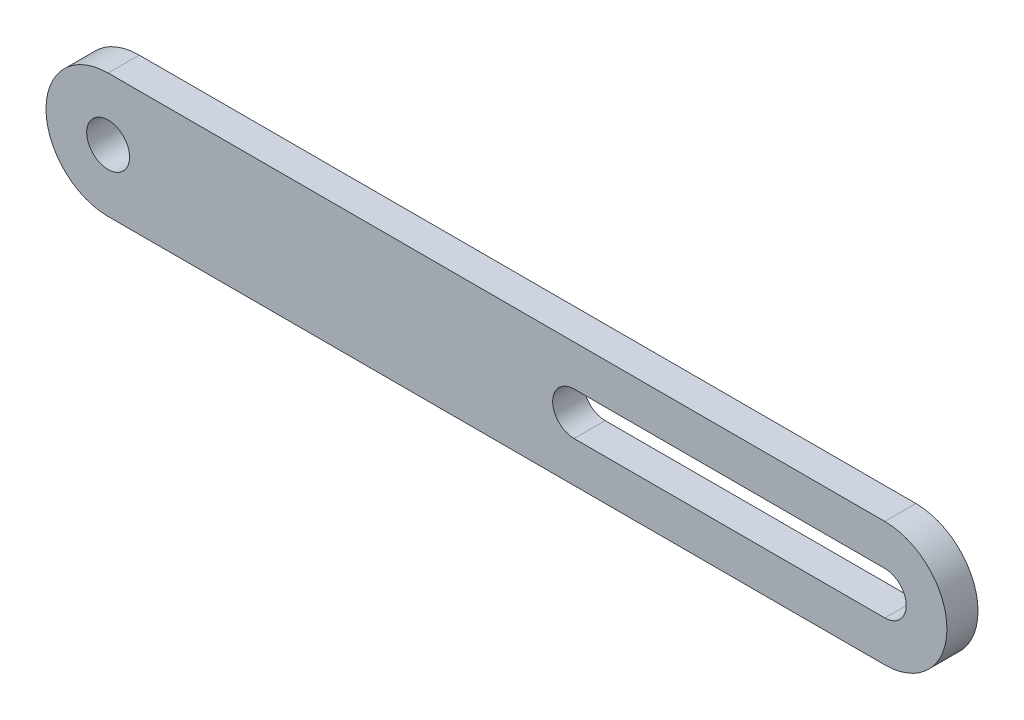
SolidWorks part; units mm, degrees
ref_plane "Front Plane" through (0, 0, 0) normal (0, 0, 1) x (1, 0, 0)
ref_plane "Top Plane" through (0, 0, 0) normal (0, 1, 0) x (1, 0, 0)
ref_plane "Right Plane" through (0, 0, 0) normal (1, 0, 0) x (0, 0, -1)
sketch "Sketch1" plane through (0, 0, 0) normal (0, 0, 1) x (1, 0, 0)
  line L0 (0, 0) -> (63.5, 0) construction
  line L1 (0, 5.08) -> (63.5, 5.08)
  line L2 (0, -5.08) -> (63.5, -5.08)
  arc A0 (0, 5.08) -> (0, -5.08) centre (0, 0) ccw
  arc A1 (63.5, -5.08) -> (63.5, 5.08) centre (63.5, 0) ccw
  point P3 (31.75, 0)
  dimension "D1" = 5.08
  dimension "D2" = 63.5
extrude "Boss-Extrude1" add sketch "Sketch1" along normal blind 2.54
sketch "Sketch2" plane through (0, 0, 2.54) normal (0, 0, 1) x (1, 0, 0)
  circle A0 centre (0, 0) radius 1.7526
  dimension "D1" = 3.5052
extrude "Cut-Extrude1" cut sketch "Sketch2" against normal through all both and the other way through all
ref_plane "Plane1" through (31.75, 0, 0) normal (1, 0, 0) x (0, 0, -1)
mirror "Mirror1" about plane through (31.75, 0, 0) normal (1, 0, 0) of "Cut-Extrude1"
sketch "Sketch4" plane through (0, 0, 2.54) normal (0, 0, 1) x (1, 0, 0)
  line L0 (63.5, 0) -> (38.0987, 0) construction
  line L1 (63.5, -1.7526) -> (38.0987, -1.7526)
  line L2 (63.5, 1.7526) -> (38.0987, 1.7526)
  arc A0 (63.5, -1.7526) -> (63.5, 1.7526) centre (63.5, 0) ccw
  arc A1 (38.0987, 1.7526) -> (38.0987, -1.7526) centre (38.0987, 0) ccw
  point P4 (50.7994, 0)
  dimension "D1" = 3.5052
extrude "Cut-Extrude2" cut sketch "Sketch4" against normal through all both and the other way through all
